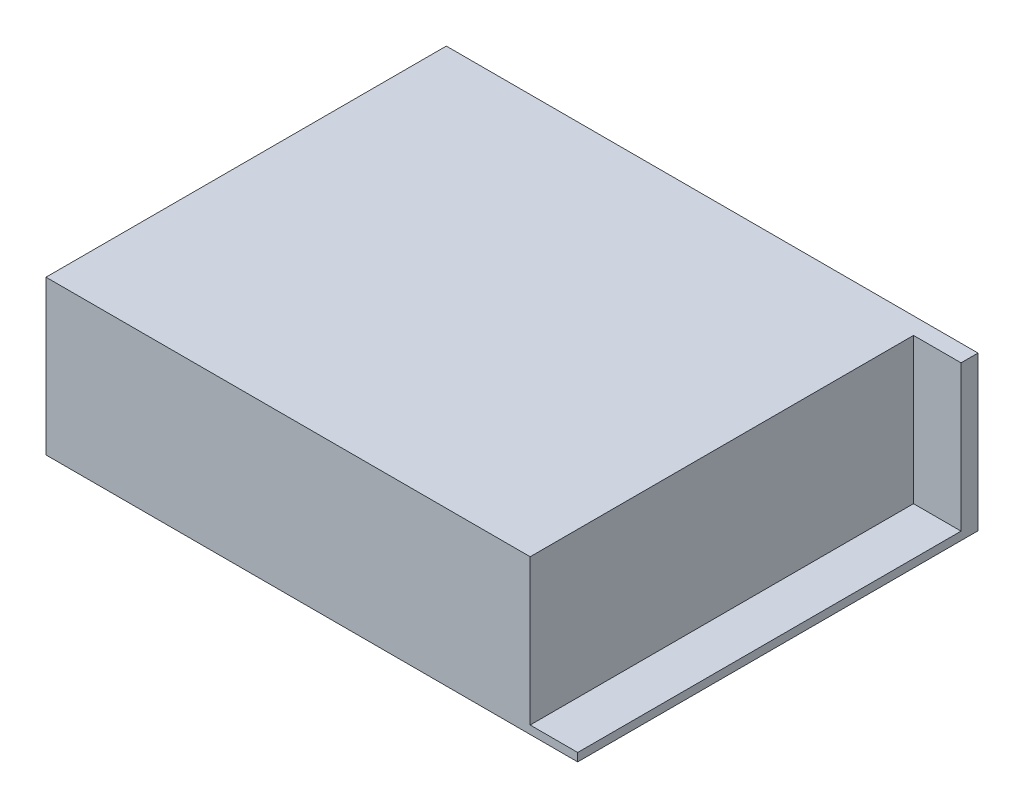
SolidWorks part; units mm, degrees
ref_plane "Front Plane" through (0, 0, 0) normal (0, 0, 1) x (1, 0, 0)
ref_plane "Top Plane" through (0, 0, 0) normal (0, 1, 0) x (1, 0, 0)
ref_plane "Right Plane" through (0, 0, 0) normal (1, 0, 0) x (0, 0, -1)
sketch "Sketch1" plane through (0, 0, 0) normal (0, 1, 0) x (1, 0, 0)
  line L1 (0, 0) -> (129.5, 0)
  line L2 (0, 0) -> (0, 97.5)
  line L3 (0, 97.5) -> (129.5, 97.5)
  line L4 (129.5, 0) -> (129.5, 97.5)
  dimension "D1" = 129.5
  dimension "D2" = 97.5
extrude "Boss-Extrude1" add sketch "Sketch1" along normal blind 37.5
hole_wizard "M3 Clearance Hole1" positions "Sketch4" profile "Sketch3" hole size "M3" standard "ANSI Metric"
sketch "Sketch4" plane through (0, 0, 0) normal (0, -1, 0) x (-1, 0, 0)
  line L0 (0, 0) -> (-129.5, 0) construction
  line L1 (-129.5, 0) -> (-129.5, 97.5) construction
  point P0 (-51.5, 63.75)
  point P2 (-51.5, 30.75)
  dimension "D1" = 30.75
  dimension "D2" = 33
  dimension "D3" = 78
sketch "Sketch3" plane through (51.5, 0, -63.75) normal (1, 0, 0) x (0, 0, -1)
  line L0 (0, 0) -> (0, 1.7585)
  line L1 (0, 1.7585) -> (1.7, 0.737)
  line L2 (1.7, 0.737) -> (1.7, 0)
  line L5 (1.7, 0) -> (0, 0)
  line L10 (0, 1.7585) -> (-1.7, 0.737) construction
  line L11 (0, -6.35) -> (0, 107.95) construction
  dimension "Hole Dia." = 3.4
  dimension "Hole Depth" = 0.737
  dimension "Drill Angle" = 118
sketch "Sketch5" plane through (0, 37.5, 0) normal (0, 1, 0) x (1, 0, 0)
  line L1 (129.5, 0) -> (117.9248, 0)
  line L2 (129.5, 0) -> (129.5, 93.3703)
  line L3 (129.5, 93.3703) -> (117.9248, 93.3703)
  line L4 (117.9248, 0) -> (117.9248, 93.3703)
extrude "Cut-Extrude1" cut sketch "Sketch5" against normal blind 35.5
